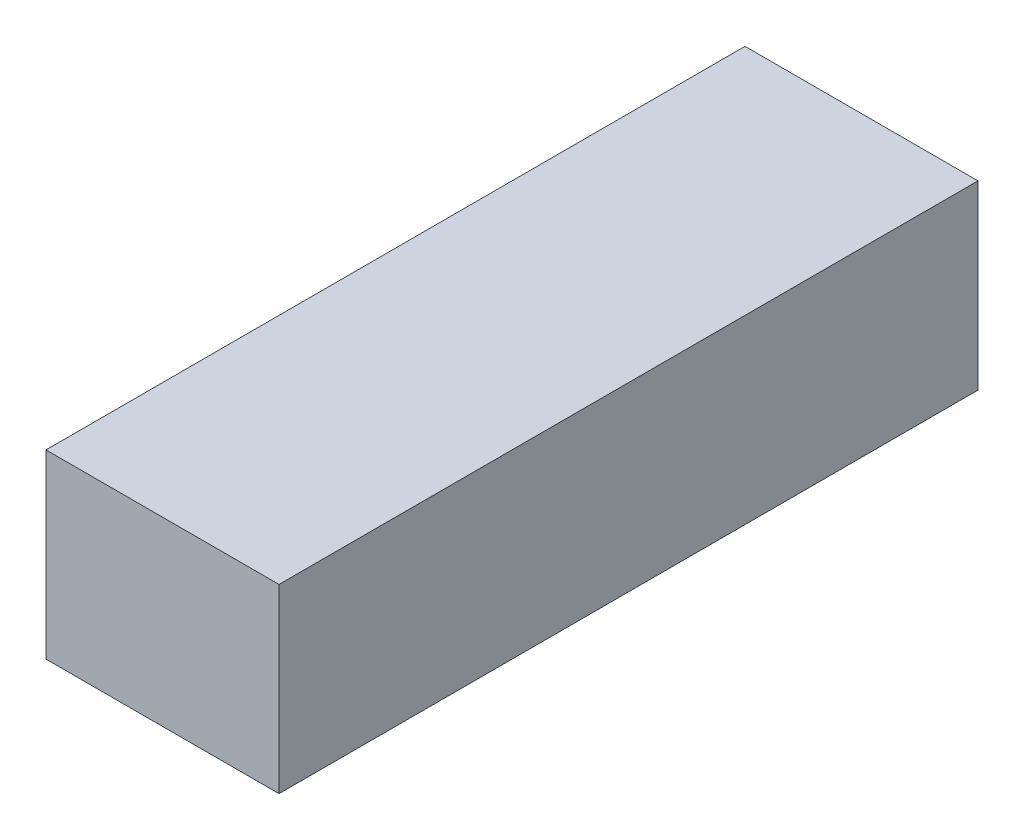
SolidWorks part; units mm, degrees
ref_plane "前视基准面" through (0, 0, 0) normal (0, 0, 1) x (1, 0, 0)
ref_plane "上视基准面" through (0, 0, 0) normal (0, 1, 0) x (1, 0, 0)
ref_plane "右视基准面" through (0, 0, 0) normal (1, 0, 0) x (0, 0, -1)
other "Configuration Table"
sketch "Sketch1" plane through (0, 0, 0) normal (0, 1, 0) x (1, 0, 0)
  line L1 (-22.5, 67.5) -> (22.5, 67.5)
  line L2 (-22.5, 67.5) -> (-22.5, -67.5)
  line L3 (-22.5, -67.5) -> (22.5, -67.5)
  line L4 (22.5, 67.5) -> (22.5, -67.5)
  line L5 (0, -67.5) -> (0, 67.5) construction
  line L6 (-22.5, 0) -> (22.5, 0) construction
  point P0 (0, 0)
  dimension "D1" = 135
  dimension "D2" = 45
extrude "Boss-Extrude1" add sketch "Sketch1" along normal blind 35
sketch "Sketch2" plane through (0, 35, 0) normal (0, 1, 0) x (1, 0, 0)
  text T0 "<b>Battery</b>" font "汉仪长仿宋体" height in points 14
